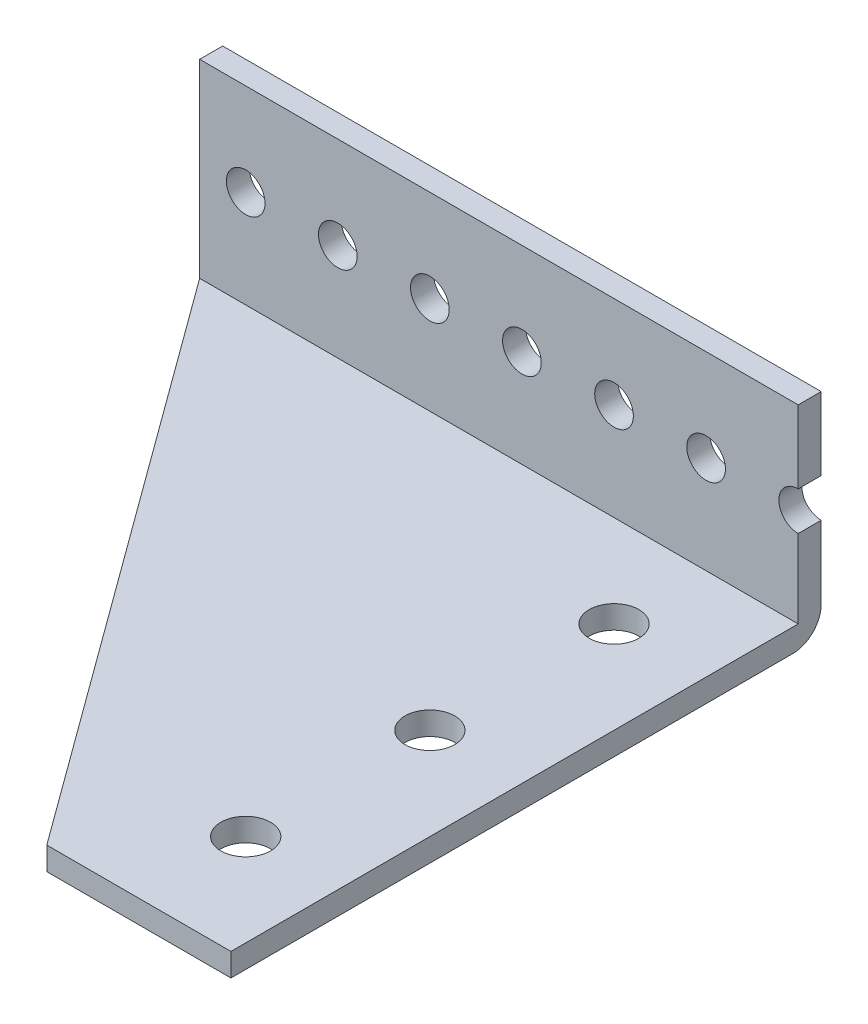
SolidWorks part; units mm, degrees
ref_plane "Front Plane" through (0, 0, 0) normal (0, 0, 1) x (1, 0, 0)
ref_plane "Top Plane" through (0, 0, 0) normal (0, 1, 0) x (1, 0, 0)
ref_plane "Right Plane" through (0, 0, 0) normal (1, 0, 0) x (0, 0, -1)
sketch "Sketch1" plane through (0, 0, 0) normal (0, 1, 0) x (1, 0, 0)
  line L0 (41.275, -40.7035) -> (41.275, 40.7035)
  line L1 (41.275, 40.7035) -> (-41.275, 40.7035)
  line L3 (-41.275, -40.7035) -> (-41.275, 40.7035)
  line L4 (-41.275, -40.7035) -> (41.275, -40.7035)
  line L5 (41.275, 40.7035) -> (-41.275, -40.7035) construction
  line L6 (0, -55) -> (0, 55) construction
  line L7 (-55, 0) -> (55, 0) construction
  point P2 (0, 0)
  dimension "D2" = 81.407
  dimension "D1" = 82.55
extrude "Boss-Extrude1" add sketch "Sketch1" along normal blind 3.175 from offset 34.925 offset against normal yes
sketch "Sketch3" plane through (0, -31.75, 0) normal (0, 1, 0) x (1, 0, 0)
  line L0 (41.275, 37.5285) -> (-41.275, 37.5285)
  line L1 (-41.275, 37.5285) -> (-41.275, 40.7035)
  line L2 (-41.275, 40.7035) -> (41.275, 40.7035)
  line L4 (41.275, 37.5285) -> (41.275, 40.7035)
  line L5 (-41.275, 40.7035) -> (-41.275, -40.7035) construction
  line L6 (41.275, -40.7035) -> (41.275, 40.7035) construction
  line L7 (41.275, 40.7035) -> (-41.275, 40.7035) construction
  dimension "D1" = 3.175
extrude "Boss-Extrude2" add sketch "Sketch3" along normal blind 50.8
hole_wizard "#10 Clearance Hole2" positions "Sketch7" profile "Sketch6" hole size "#10" standard "ANSI Inch" end condition through all
sketch "Sketch7" plane through (0, 0, -40.7035) normal (0, 0, -1) x (-1, 0, 0)
  line L2 (-41.275, -18.288) -> (34.925, -18.288) construction
  line L5 (-41.275, 7.112) -> (34.925, 7.112) construction
  line L8 (41.275, 19.05) -> (41.275, -34.925) construction
  line L9 (-41.275, 19.05) -> (-41.275, -34.925) construction
  line L10 (-41.275, 19.05) -> (41.275, 19.05) construction
  point P56 (22.225, 7.112)
  point P57 (9.525, 7.112)
  point P58 (-3.175, 7.112)
  point P59 (-15.875, 7.112)
  point P61 (-28.575, 7.112)
  point P118 (22.225, -18.288)
  point P119 (9.525, -18.288)
  point P120 (-3.175, -18.288)
  point P121 (-15.875, -18.288)
  point P123 (-28.575, -18.288)
  point P157 (34.925, 7.112)
  point P159 (34.925, -18.288)
  point P185 (-41.275, 7.112)
  point P189 (-41.275, -18.288)
  dimension "D1" = 6.35
  dimension "D2" = 11.938
  dimension "D3" = 12.7
  dimension "D4" = 25.4
  dimension "D5" = 12.7
  dimension "D6" = 12.7
  dimension "D7" = 12.7
  dimension "D8" = 12.7
  dimension "D10" = 12.7
sketch "Sketch6" plane through (-22.225, 7.112, -40.7035) normal (1, 0, 0) x (0, 1, 0)
  line L0 (0, 0) -> (0, 81.407)
  line L1 (0, 81.407) -> (2.667, 81.407)
  line L2 (2.667, 81.407) -> (2.667, 0)
  line L5 (2.667, 0) -> (0, 0)
  line L11 (0, -6.35) -> (0, 107.95) construction
  dimension "Thru Hole Dia." = 5.334
  dimension "Thru Hole Depth" = 81.407
chamfer "Chamfer1" distance 3.175 angle 45 1 edges at (-41.275, 19.05, -39.116)
fillet "Fillet2" radius 3.937 1 edges at (0, -34.925, -40.7035)
sketch "Sketch9" plane through (0, -34.925, 0) normal (0, -1, 0) x (1, 0, 0)
  line L2 (41.275, -40.7035) -> (-41.275, -40.7035) construction
  line L3 (41.275, 40.7035) -> (41.275, -36.7665) construction
  line L5 (-41.275, -37.5285) -> (-41.275, 40.7035)
  line L6 (-41.275, 40.7035) -> (41.275, 40.7035) construction
  line L7 (28.575, -40.7035) -> (28.575, 40.7035) construction
  line L10 (-41.275, -37.5285) -> (15.875, 40.7035)
  line L11 (15.875, 40.7035) -> (-41.275, 40.7035)
  line L12 (41.275, 40.7035) -> (41.275, -36.7665) construction
  line L14 (-41.275, -36.7665) -> (-41.275, 40.7035) construction
  line L16 (-41.275, -37.5285) -> (41.275, -37.5285) construction
  circle A0 centre (34.925, 1.4605) radius 3.429 construction
  circle A1 centre (34.925, -11.2395) radius 3.429 construction
  circle A2 centre (34.925, -23.9395) radius 3.429 construction
  circle A3 centre (28.575, -24.8285) radius 3.429
  circle A7 centre (28.575, 0.5715) radius 3.429
  circle A8 centre (28.575, 25.9715) radius 3.429
  dimension "D3" = 6.858
  dimension "D7" = 16.764
  dimension "D9" = 6.858
  dimension "D10" = 0
  dimension "D11" = 3
  dimension "D12" = 25.4
  dimension "D2" = 12.7
  dimension "D4" = 12.7
  dimension "D5" = 12.7
  dimension "D6" = 6.35
  dimension "D8" = 25.4
  dimension "D13" = 12.7
extrude "Cut-Extrude2" cut sketch "Sketch9" against normal through all
sketch "Sketch10" plane through (0, 0, -40.7035) normal (0, 0, -1) x (-1, 0, 0)
  line L0 (-41.275, -5.588) -> (41.275, -5.588)
  line L1 (-41.275, 4.445) -> (-41.275, -15.621) construction
  line L2 (41.275, 15.875) -> (41.275, -30.988) construction
  line L3 (41.275, -5.588) -> (41.275, 19.05)
  line L4 (41.275, 19.05) -> (-41.275, 19.05)
  line L5 (-41.275, 19.05) -> (-41.275, -5.588)
extrude "Cut-Extrude3" cut sketch "Sketch10" against normal through all
